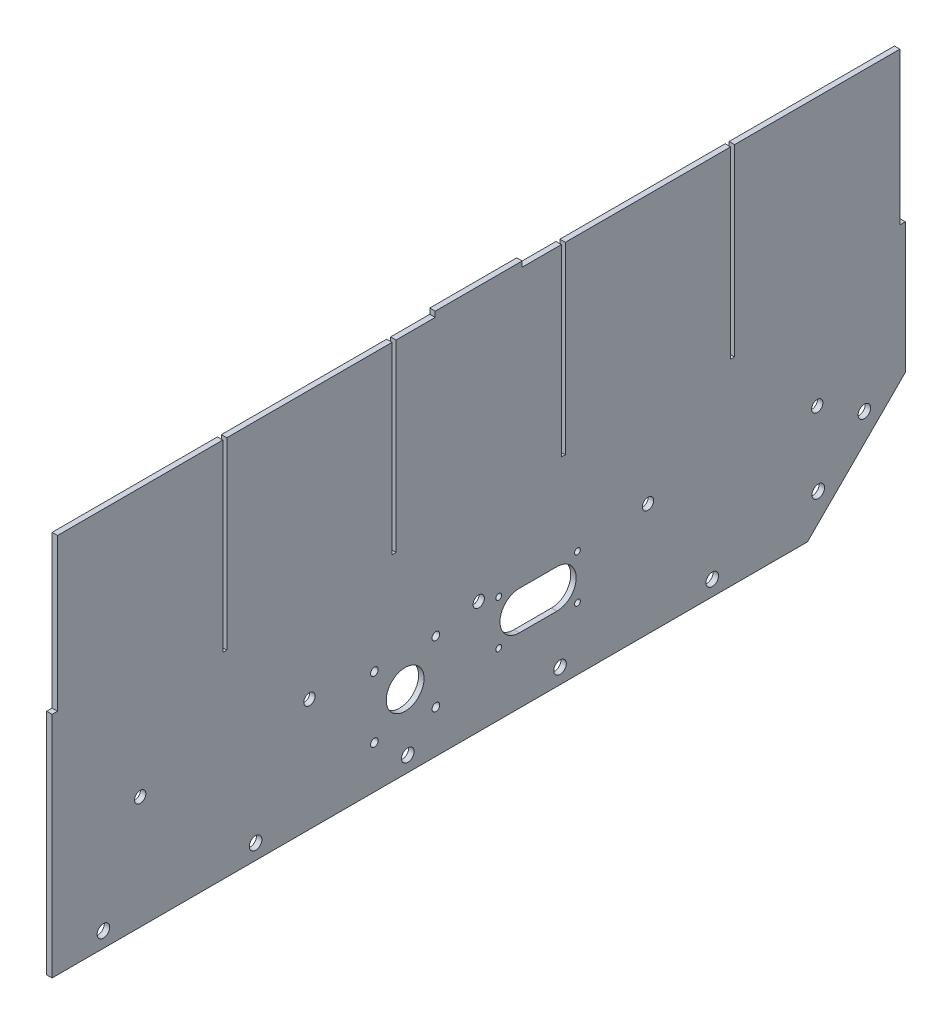
SolidWorks part; units mm, degrees
material "6061-T6 (SS)"
ref_plane "X-Y Datum" through (0, 0, 0) normal (0, 0, 1) x (1, 0, 0)
ref_plane "X-Z Datum" through (0, 0, 0) normal (0, 1, 0) x (1, 0, 0)
ref_plane "Y-Z Datum" through (0, 0, 0) normal (1, 0, 0) x (0, 0, -1)
sketch "Sketch1" plane through (0, 0, 0) normal (1, 0, 0) x (0, 0, -1)
  line L1 (-249.174, 82.55) -> (249.174, 82.55)
  line L2 (-249.174, 82.55) -> (-249.174, -82.55)
  line L3 (-249.174, -82.55) -> (249.174, -82.55)
  line L4 (249.174, 82.55) -> (249.174, -82.55)
  line L5 (-249.174, 82.55) -> (249.174, -82.55) construction
  line L6 (-249.174, -82.55) -> (249.174, 82.55) construction
  point P0 (0, 0)
  dimension "D1" = 165.1
  dimension "D2" = 498.348
extrude "Boss-Extrude1" add sketch "Sketch1" along normal mid plane 3.175
sketch "Sketch2" plane through (1.5875, 0, 0) normal (1, 0, 0) x (0, 0, -1)
  line L2 (249.174, -82.55) -> (192.024, -139.7)
  line L5 (-249.174, -82.55) -> (249.174, -82.55) construction
  line L6 (-249.174, -82.55) -> (249.174, -82.55)
  line L8 (192.024, -139.7) -> (-249.174, -139.7)
  line L9 (-249.174, -139.7) -> (-249.174, -82.55)
  line L11 (-249.174, 82.55) -> (-249.174, -82.55) construction
  line L12 (249.174, -82.55) -> (249.174, 82.55) construction
  dimension "D1" = 45
  dimension "D5" = 57.15
extrude "Boss-Extrude2" add sketch "Sketch2" against normal blind 3.175
sketch "Sketch3" plane through (-1.5875, 0, 0) normal (-1, 0, 0) x (0, 0, 1)
  line L0 (219.202, -139.7) -> (219.202, -130.81)
  line L1 (-192.024, -139.7) -> (249.174, -139.7) construction
  line L2 (219.202, -130.81) -> (249.174, -130.81)
  line L3 (249.174, 82.55) -> (249.174, -139.7) construction
  circle A0 centre (219.202, -130.81) radius 3.675
  dimension "D1" = 7.35
extrude "Cut-Extrude1" cut sketch "Sketch3" against normal through all contours L0 A0 L2 | L2 A0 L0
pattern_linear "LPattern1" count 5 spacing 88.9 along (0, 0, -1) of "Cut-Extrude1"
sketch "Sketch4" plane through (-1.5875, 0, 0) normal (-1, 0, 0) x (0, 0, 1)
  line L0 (-206.3924, -125.3316) -> (-198.3102, -117.2494)
  line L1 (-249.174, -82.55) -> (-192.024, -139.7) construction
  line L2 (-192.024, -139.7) -> (-183.9418, -131.6178)
  line L3 (-183.9418, -131.6178) -> (-198.3102, -117.2494)
  circle A0 centre (-198.3102, -117.2494) radius 3.675
extrude "Cut-Extrude2" cut sketch "Sketch4" against normal through all and the other way through all contours L3 A0 L0 | L0 A0 L3
pattern_linear "LPattern2" count 2 spacing 38.1 along (0, 0.7071, -0.7071) of "Cut-Extrude2"
sketch "Sketch5" plane through (1.5875, 0, 0) normal (1, 0, 0) x (0, 0, -1)
  line L1 (249.174, 82.55) -> (245.999, 82.55)
  line L2 (249.174, 82.55) -> (249.174, -6.35)
  line L3 (249.174, -6.35) -> (245.999, -6.35)
  line L4 (245.999, 82.55) -> (245.999, -6.35)
  line L5 (-249.174, 82.55) -> (-245.999, 82.55)
  line L6 (-249.174, 82.55) -> (-249.174, -6.35)
  line L7 (-249.174, -6.35) -> (-245.999, -6.35)
  line L8 (-245.999, 82.55) -> (-245.999, -6.35)
  dimension "D1" = 3.175
  dimension "D2" = 88.9
  dimension "D3" = 3.175
  dimension "D4" = 88.9
extrude "Cut-Extrude3" cut sketch "Sketch5" against normal through all
sketch "Sketch6" plane through (1.5875, 0, 0) normal (1, 0, 0) x (0, 0, -1)
  line L0 (122.174, 82.55) -> (249.174, 82.55) construction
  line L1 (149.4282, -24.892) -> (149.4282, 82.55) construction
  line L2 (122.174, 82.55) -> (249.174, 82.55)
  line L3 (149.4282, -24.892) -> (149.4282, 82.55)
  line L5 (149.4282, 82.55) -> (147.1422, 82.55)
  line L6 (149.4282, 82.55) -> (149.4282, -24.892)
  line L7 (149.4282, -24.892) -> (147.1422, -24.892)
  line L8 (147.1422, 82.55) -> (147.1422, -24.892)
  dimension "D1" = 2.286
  dimension "D2" = 107.442
extrude "Cut-Extrude4" cut sketch "Sketch6" against normal through all contours L2 L8 L7 L3
pattern_linear "LPattern3" count 4 spacing 98.8568 along (0, 0, 1) of "Cut-Extrude4"
sketch "Sketch8" plane through (1.5875, 0, 0) normal (1, 0, 0) x (0, 0, -1)
  line L0 (122.174, 85.725) -> (25.4, 85.725) construction
  line L1 (25.4, 82.55) -> (-25.4, 82.55)
  line L2 (25.4, 82.55) -> (25.4, 85.725)
  line L3 (25.4, 85.725) -> (-25.4, 85.725)
  line L4 (-25.4, 82.55) -> (-25.4, 85.725)
  line L5 (25.4, 82.55) -> (-25.4, 85.725) construction
  line L6 (25.4, 85.725) -> (-25.4, 82.55) construction
  point P0 (0, 84.1375)
  dimension "D1" = 3.175
  dimension "D2" = 50.8
extrude "Boss-Extrude3" add sketch "Sketch8" against normal blind 3.175
sketch "Sketch9" plane through (1.5875, 0, 0) normal (1, 0, 0) x (0, 0, -1)
  line L0 (-249.174, -6.35) -> (-249.174, -139.7) construction
  line L1 (192.024, -139.7) -> (-249.174, -139.7) construction
  circle A0 centre (-42.9768, -96.7994) radius 11.05
  dimension "D3" = 22.1
  dimension "D1" = 206.1972
  dimension "D2" = 42.9006
extrude "Cut-Extrude5" cut sketch "Sketch9" against normal through all
sketch "Sketch10" plane through (1.5875, 0, 0) normal (1, 0, 0) x (0, 0, -1)
  line L0 (192.024, -139.7) -> (-249.174, -139.7) construction
  circle A0 centre (0, -73.8124) radius 3
  dimension "D2" = 6
  dimension "D1" = 65.8876
hole_wizard "M6 Clearance Hole1" positions "Sketch11" profile "Sketch12" hole size "M6" standard "ANSI Metric" end condition through all
sketch "Sketch11" plane through (1.5875, 0, 0) normal (1, 0, 0) x (0, 0, -1)
  point P0 (0, -73.8124)
sketch "Sketch12" plane through (1.5875, -73.8124, 0) normal (0, 1, 0) x (0, 0, -1)
  line L0 (0, 0) -> (0, 3.175)
  line L1 (0, 3.175) -> (3.3, 3.175)
  line L2 (3.3, 3.175) -> (3.3, 0)
  line L5 (3.3, 0) -> (0, 0)
  line L11 (0, -6.35) -> (0, 107.95) construction
  dimension "Thru Hole Dia." = 6.6
  dimension "Thru Hole Depth" = 3.175
pattern_linear "LPattern4" count 3 spacing 98.8568 along (0, 0, 1) count 3 spacing 98.8568 along (0, 0, -1) of "M6 Clearance Hole1"
sketch "Sketch14" plane through (1.5875, 0, 0) normal (1, 0, 0) x (0, 0, -1)
  line L0 (192.024, -139.7) -> (-249.174, -139.7) construction
  line L1 (57.674, -103.315) -> (11.674, -103.315)
  line L2 (57.674, -103.315) -> (57.674, -77.315)
  line L3 (57.674, -77.315) -> (11.674, -77.315)
  line L4 (11.674, -103.315) -> (11.674, -77.315)
  line L5 (57.674, -103.315) -> (11.674, -77.315) construction
  line L6 (57.674, -77.315) -> (11.674, -103.315) construction
  line L7 (249.174, -82.55) -> (249.174, -6.35) construction
  line L8 (57.674, -90.315) -> (11.674, -90.315) construction
  line L9 (-25.0163, -114.7599) -> (-60.9373, -114.7599)
  line L10 (-25.0163, -114.7599) -> (-25.0163, -78.8389)
  line L11 (-25.0163, -78.8389) -> (-60.9373, -78.8389)
  line L12 (-60.9373, -114.7599) -> (-60.9373, -78.8389)
  line L13 (-25.0163, -114.7599) -> (-60.9373, -78.8389) construction
  line L14 (-25.0163, -78.8389) -> (-60.9373, -114.7599) construction
  line L15 (45.674, -90.315) -> (23.674, -90.315)
  line L16 (45.674, -101.565) -> (23.674, -101.565)
  line L17 (45.674, -79.065) -> (23.674, -79.065)
  arc A1 (45.674, -101.565) -> (45.674, -79.065) centre (45.674, -90.315) ccw
  arc A2 (23.674, -79.065) -> (23.674, -101.565) centre (23.674, -90.315) ccw
  point P0 (34.674, -90.315)
  point P10 (-42.9768, -96.7994)
  point P20 (34.674, -90.315)
  dimension "D7" = 11.25
  dimension "D1" = 46
  dimension "D2" = 26
  dimension "D3" = 36.385
  dimension "D4" = 191.5
  dimension "D5" = 35.921
  dimension "D6" = 22
hole_wizard "M3 Clearance Hole1" positions "Sketch15" profile "Sketch16" hole size "M3" standard "ANSI Metric" end condition through all
sketch "Sketch15" plane through (1.5875, 0, 0) normal (1, 0, 0) x (0, 0, -1)
  point P0 (11.674, -77.315)
  point P3 (11.674, -103.315)
  point P6 (57.674, -103.315)
  point P9 (57.674, -77.315)
sketch "Sketch16" plane through (1.5875, -77.315, -11.674) normal (0, 1, 0) x (0, 0, -1)
  line L0 (0, 0) -> (0, 3.175)
  line L1 (0, 3.175) -> (1.7, 3.175)
  line L2 (1.7, 3.175) -> (1.7, 0)
  line L5 (1.7, 0) -> (0, 0)
  line L11 (0, -6.35) -> (0, 107.95) construction
  dimension "Thru Hole Dia." = 3.4
  dimension "Thru Hole Depth" = 3.175
hole_wizard "M4 Clearance Hole1" positions "Sketch17" profile "Sketch18" hole size "M4" standard "ANSI Metric" end condition through all
sketch "Sketch17" plane through (1.5875, 0, 0) normal (1, 0, 0) x (0, 0, -1)
  point P0 (-25.0163, -78.8389)
  point P3 (-60.9373, -78.8389)
  point P6 (-60.9373, -114.7599)
  point P9 (-25.0163, -114.7599)
sketch "Sketch18" plane through (1.5875, -78.8389, 25.0163) normal (0, 1, 0) x (0, 0, -1)
  line L0 (0, 0) -> (0, 3.175)
  line L1 (0, 3.175) -> (2.25, 3.175)
  line L2 (2.25, 3.175) -> (2.25, 0)
  line L5 (2.25, 0) -> (0, 0)
  line L11 (0, -6.35) -> (0, 107.95) construction
  dimension "Thru Hole Dia." = 4.5
  dimension "Thru Hole Depth" = 3.175
extrude "Cut-Extrude6" cut sketch "Sketch14" against normal through all
